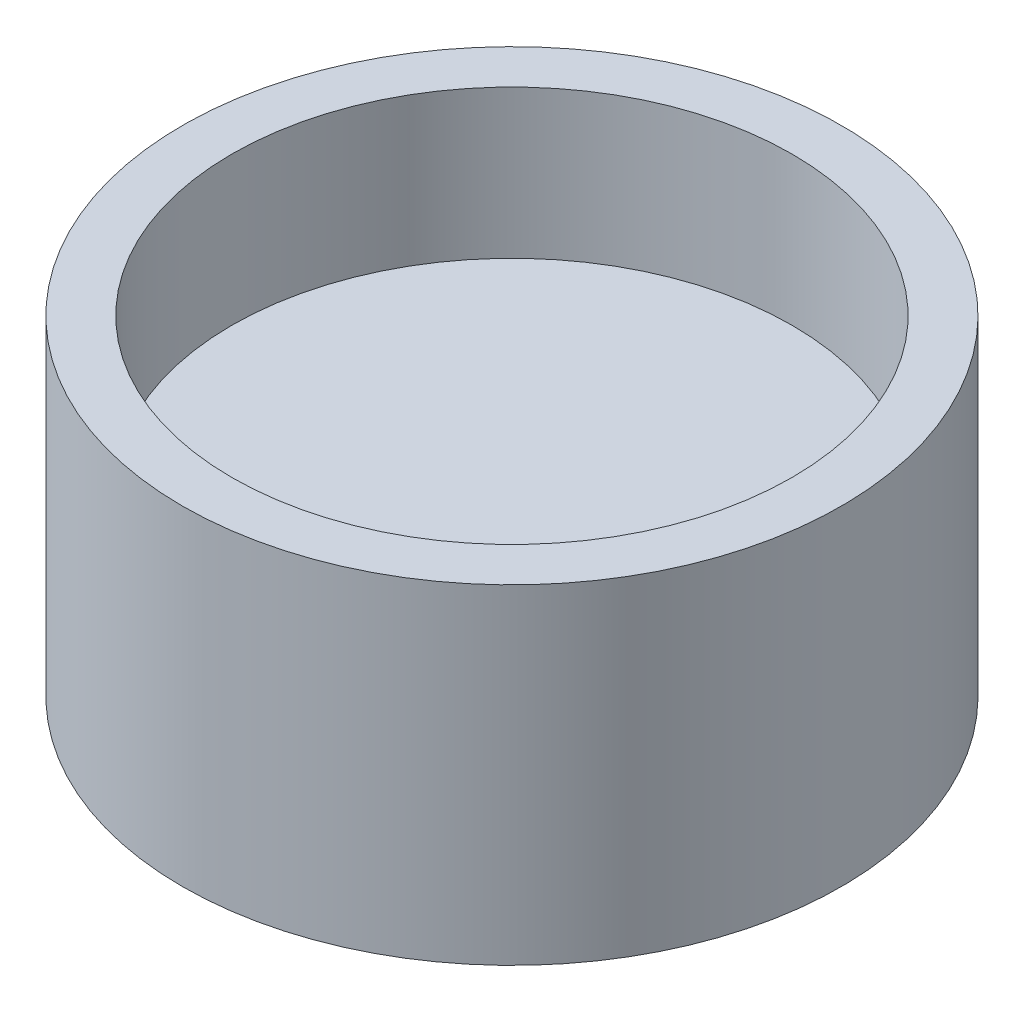
SolidWorks part; units mm, degrees
ref_plane "Front Plane" through (0, 0, 0) normal (0, 0, 1) x (1, 0, 0)
ref_plane "Top Plane" through (0, 0, 0) normal (0, 1, 0) x (1, 0, 0)
ref_plane "Right Plane" through (0, 0, 0) normal (1, 0, 0) x (0, 0, -1)
sketch "Sketch1" plane through (0, 0, 0) normal (0, 1, 0) x (1, 0, 0)
  circle A0 centre (0, 0) radius 4
  dimension "D1" = 8
extrude "Boss-Extrude1" add sketch "Sketch1" along normal blind 4
sketch "Sketch2" plane through (0, 4, 0) normal (0, 1, 0) x (1, 0, 0)
  circle A0 centre (0, 0) radius 3.4
  dimension "D1" = 6.8
extrude "Cut-Extrude1" cut sketch "Sketch2" against normal blind 1.8
